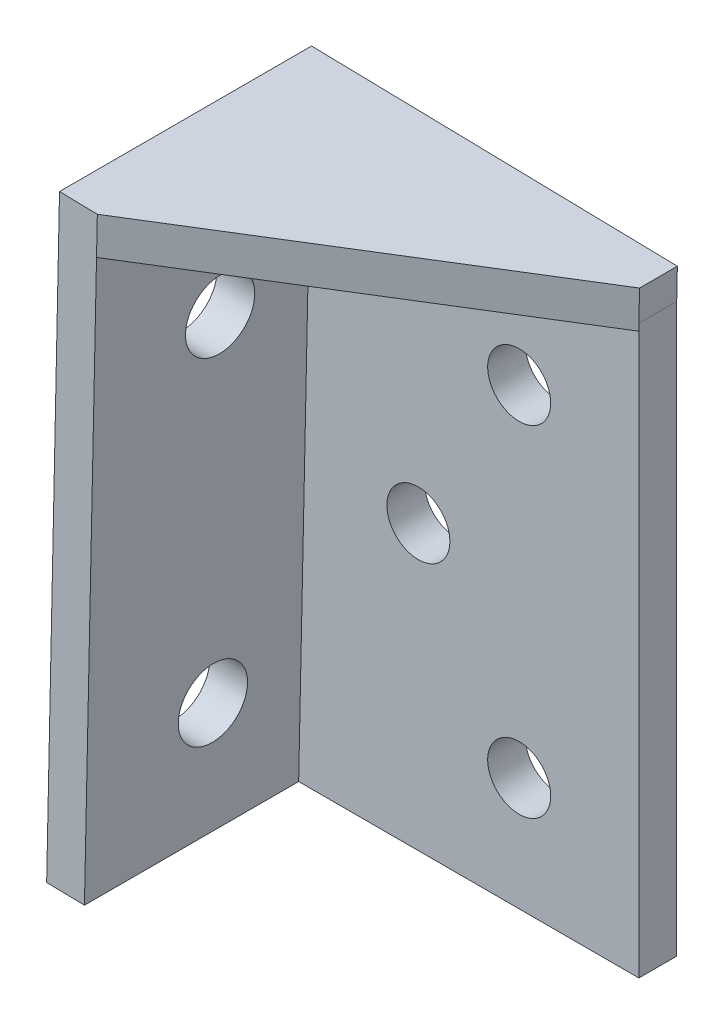
SolidWorks part; units mm, degrees
ref_plane "Front Plane" through (0, 0, 0) normal (0, 0, 1) x (1, 0, 0)
ref_plane "Top Plane" through (0, 0, 0) normal (0, 1, 0) x (1, 0, 0)
ref_plane "Right Plane" through (0, 0, 0) normal (1, 0, 0) x (0, 0, -1)
sketch "Sketch1" plane through (0, 0, 0) normal (0, 0, 1) x (1, 0, 0)
  line L0 (0, 0) -> (0.9583, 45)
  line L1 (0.9583, 45) -> (27, 45)
  line L2 (27, 45) -> (27, 0)
  line L3 (27, 0) -> (0, 0)
  line L4 (27, 22.5) -> (9.5, 22.5) construction
  line L5 (17.5, 9) -> (17.5, 36) construction
  circle A0 centre (17.5, 36) radius 2.5
  circle A1 centre (17.5, 9) radius 2.5
  circle A2 centre (9.5, 22.5) radius 2.5
  circle A3 centre (17.5, 36) radius 6 construction
  circle A4 centre (9.5, 22.5) radius 6 construction
  circle A5 centre (17.5, 9) radius 6 construction
  point P9 (17.5, 22.5)
  dimension "D2" = 5
  dimension "D4" = 12
  dimension "D1" = 91.22
  dimension "D3" = 45
  dimension "D5" = 27
  dimension "D6" = 27
  dimension "D7" = 9.5
  dimension "D8" = 17.5
extrude "Boss-Extrude1" add sketch "Sketch1" along normal blind 3
sketch "Sketch2" plane through (0, 0, 0) normal (-0.9998, 0.0213, 0) x (0, 0, 1)
  line L0 (0, 45.0102) -> (20, 45.0102)
  line L1 (20, 45.0102) -> (20, 0)
  line L2 (20, 0) -> (0, 0)
  line L3 (0, 0) -> (0, 45.0102)
  line L5 (10, 45.0102) -> (10, 0) construction
  circle A0 centre (10, 36.0102) radius 2.75
  circle A1 centre (10, 9) radius 2.75
  dimension "D2" = 5.5
  dimension "D3" = 5.5
  dimension "D1" = 20
  dimension "D4" = 10
  dimension "D5" = 9
  dimension "D6" = 9
extrude "Boss-Extrude2" add sketch "Sketch2" along normal blind 3
sketch "Sketch3" plane through (0.9583, 45, 0) normal (0.0213, 0.9998, 0) x (0.9998, -0.0213, 0)
  line L0 (0, -20) -> (26.0358, -3)
  line L1 (26.0358, -3) -> (26.0358, 0)
  line L2 (26.0358, 0) -> (-3, 0)
  line L3 (-3, 0) -> (-3, -20)
  line L4 (-3, -20) -> (0, -20)
extrude "Boss-Extrude3" add sketch "Sketch3" along normal blind 3
